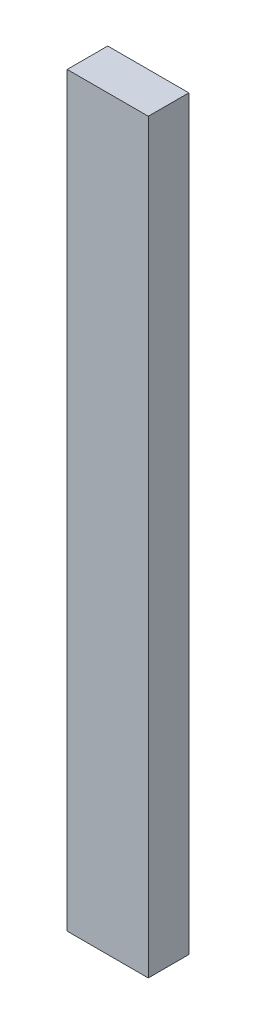
SolidWorks part; units mm, degrees
ref_plane "Front Plane" through (0, 0, 0) normal (0, 0, 1) x (1, 0, 0)
ref_plane "Top Plane" through (0, 0, 0) normal (0, 1, 0) x (1, 0, 0)
ref_plane "Right Plane" through (0, 0, 0) normal (1, 0, 0) x (0, 0, -1)
sketch "Sketch1" plane through (0, 0, 0) normal (0, 1, 0) x (1, 0, 0)
  line L1 (-0.25, 0.125) -> (0.25, 0.125)
  line L2 (-0.25, 0.125) -> (-0.25, -0.125)
  line L3 (-0.25, -0.125) -> (0.25, -0.125)
  line L4 (0.25, 0.125) -> (0.25, -0.125)
  line L5 (-0.25, 0.125) -> (0.25, -0.125) construction
  line L6 (-0.25, -0.125) -> (0.25, 0.125) construction
  point P0 (0, 0)
  dimension "D1" = 0.5
  dimension "D2" = 0.25
extrude "Boss-Extrude1" add sketch "Sketch1" along normal blind 4.6
